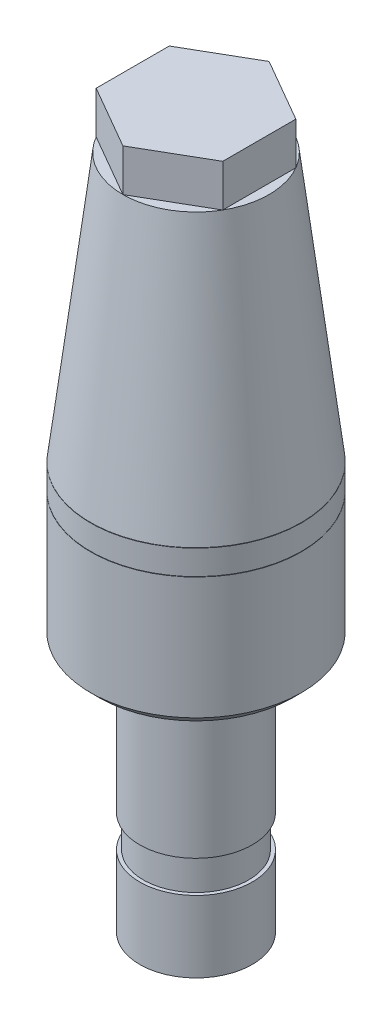
SolidWorks part; units mm, degrees
material "Brass"
ref_plane "Front Plane" through (0, 0, 0) normal (0, 0, 1) x (1, 0, 0)
ref_plane "Top Plane" through (0, 0, 0) normal (0, 1, 0) x (1, 0, 0)
ref_plane "Right Plane" through (0, 0, 0) normal (1, 0, 0) x (0, 0, -1)
sketch "Sketch1" plane through (0, 0, 0) normal (0, 0, 1) x (1, 0, 0)
  line L0 (0, 25.5) -> (0, -25.5) construction
  line L1 (-4, -25.5) -> (4, -25.5) construction
  line L2 (-7.5, 25.5) -> (7.5, 25.5) construction
  line L3 (-4.5, 22.5) -> (4.5, 22.5) construction
  point P7 (0, 22.5)
  point P8 (0, -7.65)
  point P11 (5.5, 25.5)
  point P12 (0, -8.5)
  dimension "Height" = 51
  dimension "Stem OD" = 8
  dimension "Diameter" = 15
  dimension "D2" = 3
  dimension "J" = 9
  dimension "D4" = 17.85
  dimension "L1" = 34
  dimension "D" = 11
sketch "Sketch2" plane through (0, 0, 0) normal (0, 1, 0) x (1, 0, 0)
  line L0 (0, 5.1962) -> (0, 0) construction
  line L1 (-4.5, 2.5981) -> (-4.5, -2.5981) construction
  line L2 (-4.5, -2.5981) -> (0, -5.1962) construction
  line L3 (0, -5.1962) -> (4.5, -2.5981) construction
  line L4 (4.5, -2.5981) -> (4.5, 2.5981) construction
  line L5 (4.5, 2.5981) -> (0, 5.1962) construction
  line L6 (0, 5.1962) -> (-4.5, 2.5981) construction
  line L7 (0, 0) -> (0, -5.1962) construction
  line L8 (0, 0) -> (-5.1962, 0) construction
  line L9 (-7.5, 0) -> (7.5, 0) construction
  circle A0 centre (0, 0) radius 4.5 construction
sketch "Sketch5" plane through (0, 0, 0) normal (0, 0, 1) x (1, 0, 0)
  line L0 (-4, -25.5) -> (-4, -20.42)
  line L1 (-4, -7.65) -> (-6.865, -7.65)
  line L2 (-6.865, -7.65) -> (-7.5, -7.015)
  line L3 (-7.5, -7.015) -> (-7.5, 1.6591)
  line L4 (-7.5, 3.4625) -> (-5.1962, 22.5)
  line L5 (0, 1.6591) -> (0, -25.5) construction
  line L6 (-5.1962, 22.5) -> (0, 22.5)
  line L7 (-4, -25.5) -> (-2.857, -25.5)
  line L8 (-4, -25.5) -> (4, -25.5) construction
  line L9 (-2.857, -25.5) -> (-2.857, -7.65)
  line L10 (-2.857, -7.65) -> (0, -7.65)
  line L11 (0, 25.5) -> (0, -25.5) construction
  line L12 (0, 22.5) -> (0, 3.4625) construction
  line L13 (-4, -18.134) -> (-3.746, -18.134)
  line L14 (-3.746, -18.134) -> (-3.746, -20.42)
  line L15 (-3.746, -20.42) -> (-4, -20.42)
  line L16 (-4, -18.134) -> (-4, -7.65)
  line L17 (-7.5, 1.6845) -> (-7.5, 3.4371)
  line L18 (0, 1.6591) -> (0, -7.65)
  line L19 (0, 22.5) -> (0, 3.4625)
  line L20 (-7.5, 3.4625) -> (0, 3.4625)
  line L21 (-7.5, 3.4371) -> (0, 3.4371)
  line L22 (-7.5, 1.6845) -> (0, 1.6845)
  line L23 (0, 3.4371) -> (0, 1.6845) construction
  line L24 (-7.5, 1.6591) -> (0, 1.6591)
  line L25 (0, 3.4371) -> (0, 1.6845)
  line L26 (0, 3.4625) -> (0, 3.4371) construction
  line L27 (0, 1.6845) -> (0, 1.6591) construction
  line L28 (-7.5, 3.4625) -> (-7.5, 3.4371) construction
  point P3 (0, 22.5)
  dimension "D1" = 45
  dimension "D2" = 1.143
  dimension "D3" = 0.635
  dimension "D4" = 2.286
  dimension "D5" = 5.08
  dimension "D6" = 0.254
  dimension "D7" = 11.1125
  dimension "D8" = 1.778
  dimension "D11" = 0.0254
revolve "Revolve1" add sketch "Sketch5" angle 360 about L12
sketch "Sketch3" plane through (0, 0, 0) normal (0, 1, 0) x (1, 0, 0)
  line L1 (0, 5.1962) -> (-4.5, 2.5981)
  line L2 (-4.5, 2.5981) -> (-4.5, -2.5981)
  line L3 (-4.5, -2.5981) -> (0, -5.1962)
  line L4 (0, -5.1962) -> (4.5, -2.5981)
  line L5 (4.5, -2.5981) -> (4.5, 2.5981)
  line L6 (4.5, 2.5981) -> (0, 5.1962)
  circle A0 centre (0, 0) radius 4.5 construction
  circle A1 centre (0, 0) radius 5.1962 construction
extrude "Boss-Extrude1" add sketch "Sketch3" against normal up to vertex (-22.5 mm away) from vertex at 25.5 separate body starting at point (0, 25.5, 0)
sketch "Sketch6" plane through (0, 0, 0) normal (0, 0, 1) x (1, 0, 0)
  line L0 (-2.857, -7.65) -> (-6.23, -4.277)
  line L1 (-6.23, -4.277) -> (-6.23, 3.4625)
  line L2 (-7.5, 3.4625) -> (0, 3.4625) construction
  line L3 (-6.23, 3.4625) -> (-4.0798, 21.23)
  line L4 (-4.0798, 21.23) -> (0, 21.23)
  line L5 (0, 25.5) -> (0, -25.5) construction
  line L6 (0, 21.23) -> (0, -7.65)
  line L7 (0, -7.65) -> (-2.857, -7.65)
  line L8 (-6.23, 3.4625) -> (-7.5, 3.4625) construction
  line L9 (0, 21.23) -> (0, 22.5) construction
  line L10 (-7.5, 3.4625) -> (-5.1962, 22.5) construction
  dimension "D1" = 1.27
  dimension "D2" = 45
revolve "Cut-Revolve1" cut sketch "Sketch6" angle 360 about L6
equation "\"D2@Sketch1\" = \"J@Sketch1\" / 3"
equation "\"D4@Sketch1\" = \"Height@Sketch1\" * .35"
